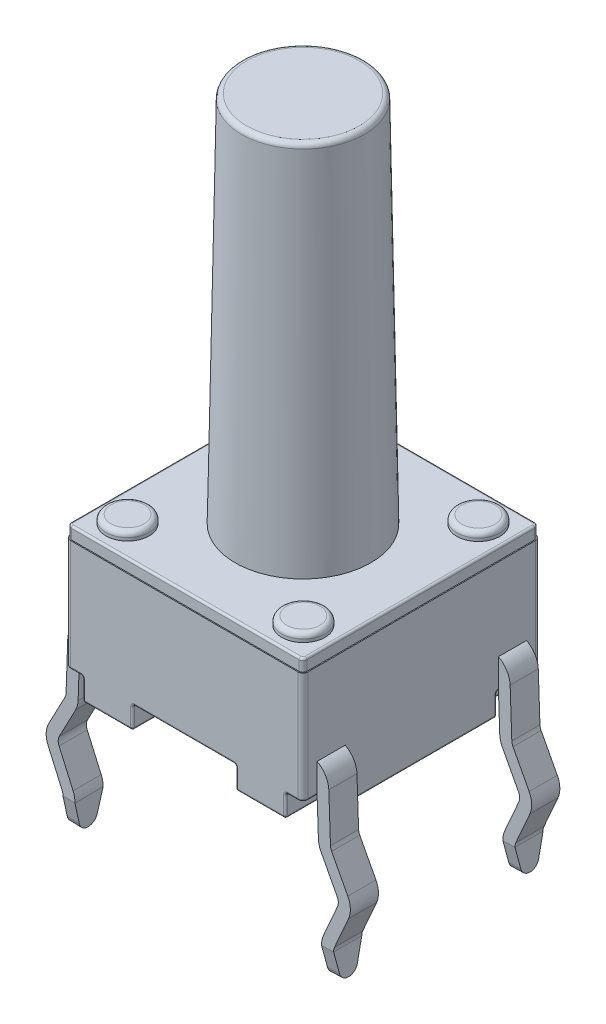
SolidWorks part; units mm, degrees
ref_plane "Front Plane" through (0, 0, 0) normal (0, 0, 1) x (1, 0, 0)
ref_plane "Top Plane" through (0, 0, 0) normal (0, 1, 0) x (1, 0, 0)
ref_plane "Right Plane" through (0, 0, 0) normal (1, 0, 0) x (0, 0, -1)
sketch "Sketch1" plane through (0, 0, 0) normal (0, 1, 0) x (1, 0, 0)
  line L1 (-3.0035, -3.0035) -> (3.0035, -3.0035)
  line L2 (-3.0035, -3.0035) -> (-3.0035, 3.0036)
  line L3 (-3.0035, 3.0036) -> (3.0035, 3.0036)
  line L4 (3.0035, -3.0035) -> (3.0035, 3.0036)
  line L5 (-3.0035, -3.0035) -> (3.0035, 3.0036) construction
  line L6 (-3.0035, 3.0036) -> (3.0035, -3.0035) construction
  point P0 (0, 0)
  dimension "D1" = 6.0071
  dimension "D2" = 6.0071
extrude "Boss-Extrude1" add sketch "Sketch1" along normal blind 2.8194 from offset 0.5588
fillet "Fillet1" radius 0.127 4 edges at (-3.0035, 1.9685, 3.0035) (-3.0035, 1.9685, -3.0036) (3.0035, 1.9685, -3.0036) (3.0035, 1.9685, 3.0035)
sketch "Sketch2" plane through (0, 3.3782, 0) normal (0, -1, 0) x (-1, 0, 0)
  line L8 (2.9781, -2.8765) -> (2.9781, 2.8765)
  line L9 (-2.8765, -2.9781) -> (2.8765, -2.9781)
  line L10 (-2.9781, 2.8765) -> (-2.9781, -2.8765)
  line L11 (2.8765, 2.9782) -> (-2.8765, 2.9782)
  line L12 (2.9781, -2.8765) -> (2.9781, 2.8765)
  line L13 (-2.8765, -2.9781) -> (2.8765, -2.9781)
  line L14 (-2.9781, 2.8765) -> (-2.9781, -2.8765)
  line L15 (2.8765, 2.9782) -> (-2.8765, 2.9782)
  arc A8 (2.8765, -2.9781) -> (2.9781, -2.8765) centre (2.8765, -2.8765) ccw
  arc A9 (-2.9781, -2.8765) -> (-2.8765, -2.9781) centre (-2.8765, -2.8765) ccw
  arc A10 (-2.8765, 2.9782) -> (-2.9781, 2.8765) centre (-2.8765, 2.8766) ccw
  arc A11 (2.9781, 2.8765) -> (2.8765, 2.9782) centre (2.8765, 2.8765) ccw
  arc A12 (2.8765, -2.9781) -> (2.9781, -2.8765) centre (2.8765, -2.8765) ccw
  arc A13 (-2.9781, -2.8765) -> (-2.8765, -2.9781) centre (-2.8765, -2.8765) ccw
  arc A14 (-2.8765, 2.9782) -> (-2.9781, 2.8765) centre (-2.8765, 2.8766) ccw
  arc A15 (2.9781, 2.8765) -> (2.8765, 2.9782) centre (2.8765, 2.8765) ccw
  dimension "D1" = 0.0254
extrude "Boss-Extrude2" add sketch "Sketch2" against normal blind 0.3048
sketch "Sketch3" plane through (0, 0, 0) normal (0, 1, 0) x (1, 0, 0)
  line L0 (-2.5662, -3.0035) -> (-2.5662, -1.8948)
  line L1 (-2.8765, -3.0035) -> (2.8765, -3.0035) construction
  line L2 (-2.5662, -1.8948) -> (-3.0035, -1.8948)
  line L3 (-3.0035, 2.8765) -> (-3.0035, -2.8765) construction
  line L4 (-2.4413, -0.5609) -> (-1.3018, -0.5609)
  line L5 (-1.3018, -0.5609) -> (-1.3017, -3.0035)
  line L6 (-2.4413, -0.5609) -> (-2.4413, 0.5609)
  line L7 (-2.5662, -3.0035) -> (-1.3017, -3.0035)
  line L8 (-3.0035, -1.8948) -> (-3.0035, 1.8948)
  line L9 (-2.4413, 0) -> (-3.0035, 0) construction
  line L10 (-2.5662, 3.0036) -> (-1.3017, 3.0035)
  line L11 (-1.3017, 0.5609) -> (-1.3017, 3.0035)
  line L12 (-2.4413, 0.5609) -> (-1.3017, 0.5609)
  line L13 (-2.5662, 1.8948) -> (-3.0035, 1.8948)
  line L14 (-2.5662, 3.0036) -> (-2.5662, 1.8948)
  line L15 (0, -3.0035) -> (0, 3.0036) construction
  line L16 (2.8765, 3.0036) -> (-2.8765, 3.0036) construction
  line L17 (2.4413, 0) -> (3.0035, 0) construction
  line L18 (2.5662, 3.0035) -> (2.5662, 1.8948)
  line L19 (2.5662, 1.8948) -> (3.0035, 1.8948)
  line L20 (2.4413, 0.5609) -> (1.3017, 0.5609)
  line L21 (1.3017, 0.5609) -> (1.3017, 3.0035)
  line L22 (2.5662, 3.0035) -> (1.3017, 3.0035)
  line L23 (3.0035, -1.8948) -> (3.0035, 1.8948)
  line L24 (2.5662, -3.0036) -> (1.3017, -3.0036)
  line L25 (2.4413, -0.5609) -> (2.4413, 0.5609)
  line L26 (1.3017, -0.5609) -> (1.3017, -3.0036)
  line L27 (2.4413, -0.5609) -> (1.3017, -0.5609)
  line L28 (2.5662, -1.8948) -> (3.0035, -1.8948)
  line L29 (2.5662, -3.0036) -> (2.5662, -1.8948)
  dimension "D1" = 1.7018
extrude "Boss-Extrude3" add sketch "Sketch3" along normal up to next
sketch "Sketch4" plane through (0, 3.683, 0) normal (0, 1, 0) x (1, 0, 0)
  line L1 (-2.2217, -2.2129) -> (2.2217, -2.2129) construction
  line L2 (-2.2217, -2.2129) -> (-2.2217, 2.2129) construction
  line L3 (-2.2217, 2.2129) -> (2.2217, 2.2129) construction
  line L4 (2.2217, -2.2129) -> (2.2217, 2.2129) construction
  line L5 (-2.2217, -2.2129) -> (2.2217, 2.2129) construction
  line L6 (-2.2217, 2.2129) -> (2.2217, -2.2129) construction
  circle A0 centre (2.2217, 2.2129) radius 0.5461
  circle A1 centre (-2.2217, 2.2129) radius 0.5461
  circle A2 centre (-2.2217, -2.2129) radius 0.5461
  circle A3 centre (2.2217, -2.2129) radius 0.5461
  point P0 (0, 0)
  dimension "D1" = 1.0922
extrude "Boss-Extrude4" add sketch "Sketch4" along normal blind 0.2032
sketch "Sketch5" plane through (0, 3.683, 0) normal (0, 1, 0) x (1, 0, 0)
  circle A0 centre (0, 0) radius 1.7145
  dimension "D1" = 3.429
extrude "Boss-Extrude5" add sketch "Sketch5" along normal blind 9.4234 draft 1
fillet "Fillet2" radius 0.127 5 edges at (-2.2217, 3.8862, -1.6668) (-2.2217, 3.8862, 2.759) (2.2217, 3.8862, -1.6668) (2.2217, 3.8862, 2.759) (0, 13.1064, 1.55)
fillet "Fillet3" radius 0.0508 88 edges at (2.9664, 0.5588, 2.9664) (2.9664, 0.5588, -2.9664) (-2.9664, 0.5588, -2.9664) (-2.9664, 0.5588, 2.9664) (3.0035, 0.5588, 2.3857) (3.0035, 0.5588, -2.3857) (1.3017, 0.2794, 3.0036) (1.3017, 0.2794, -3.0035) (2.9484, 3.683, -2.9484) (0, 3.683, -2.9782) (-2.9484, 3.683, -2.9484) (-2.9781, 3.683, 0) (-2.9484, 3.683, 2.9484) (0, 3.683, 2.9781) (2.9484, 3.683, 2.9484) (2.4413, 0.2794, 0.5609) (1.3017, 0.2794, 0.5609) (1.3017, 0.2794, -0.5609) (2.4413, 0.2794, -0.5609) (-1.3018, 0.2794, 0.5609) (-2.4413, 0.2794, 0.5609) (-2.4413, 0.2794, -0.5609) (-1.3017, 0.2794, -0.5609) (2.7849, 0.5588, 1.8948) (3.0035, 0.2794, 1.8948) (2.5662, 0.2794, 3.0036) (2.5662, 0.5588, 2.4492) (2.5662, 0.2794, 1.8948) (3.0035, 0.2794, -1.8948) (2.7849, 0.5588, -1.8948) (2.5662, 0.2794, -1.8948) (2.5662, 0.5588, -2.4492) (2.5662, 0.2794, -3.0035) (-2.5662, 0.2794, -1.8948) (-2.5662, 0.2794, 1.8948) (-1.8715, 0.5588, -0.5609) (-2.4413, 0.5588, 0) (-1.8715, 0.5588, 0.5609) (1.3017, 0.5588, 1.7822) (1.8715, 0.5588, 0.5609) (2.4413, 0.5588, 0) (1.8715, 0.5588, -0.5609) (1.3017, 0.5588, -1.7822) (-1.3017, 0, 1.7822) (-1.8715, 0, 0.5609) (-2.4413, 0, 0) (-1.8715, 0, -0.5609) (-1.3017, 0, -1.7822) (-1.934, 0, -3.0035) (-2.5662, 0, -2.4492) (-2.7849, 0, -1.8948) (-3.0035, 0, 0) (-2.7849, 0, 1.8948) (-2.5662, 0, 2.4492) (-1.934, 0, 3.0035) (1.3017, 0, -1.7822) (1.8715, 0, -0.5609) (2.4413, 0, 0) (1.8715, 0, 0.5609) (1.3017, 0, 1.7822) (1.934, 0, 3.0036) (2.5662, 0, 2.4492) (2.7849, 0, 1.8948) (3.0035, 0, 0) (2.7849, 0, -1.8948) (2.5662, 0, -2.4492) (1.934, 0, -3.0035) (2.9781, 3.683, 0)
sketch "Sketch6" plane through (0, 0, 3.0035) normal (0, 0, 1) x (1, 0, 0)
  line L0 (-2.9873, 1.0641) -> (-3.0423, -0.5107)
  line L1 (-3.0423, -0.5107) -> (-3.5687, -1.5089)
  line L2 (-3.5687, -1.5089) -> (-3.1132, -2.5415)
  line L3 (-3.1132, -2.5415) -> (-3.1424, -3.3782)
  line L4 (-2.9873, 1.0641) -> (-2.5265, 1.0641)
  line L5 (-1.3525, 0) -> (-2.5154, 0) construction
  dimension "D1" = 4.445
  dimension "D2" = 3.3782
  dimension "D3" = 3.0226
  dimension "D4" = 3.5687
  dimension "D5" = 2.032
  dimension "D6" = 1.5748
  dimension "D7" = 92
extrude "Extrude-Thin1" add sketch "Sketch6" against normal blind 0.7112 from offset 0.3556 thin offset against normal yes
sketch "Sketch9" plane through (-3.3254, 0.1161, 0) normal (-0.9994, 0.0349, 0) x (0, 0, 1)
  line L0 (2.6479, -2.7766) -> (2.5175, -3.3091)
  line L1 (2.0672, -3.3091) -> (1.9367, -2.7766)
  line L2 (1.9367, -3.4858) -> (2.6479, -3.4858) construction
  line L3 (2.6479, -2.7766) -> (2.6479, -3.4858)
  line L4 (2.6479, -3.4858) -> (1.9367, -3.4858)
  line L5 (1.9367, -3.4858) -> (1.9367, -2.7766)
  arc A0 (2.5175, -3.3091) -> (2.0672, -3.3091) centre (2.2923, -3.254) cw
  line M1 (2.6479, -3.4858) -> (2.6479, -2.7766)
  line M3 (1.9367, -2.7766) -> (1.9367, -3.4858)
  line M4 (1.9367, -3.4858) -> (2.6479, -3.4858)
extrude "Cut-Extrude1" cut sketch "Sketch9" against normal blind 0.7112 contours L0 A0 L4 M1 | A0 L1 M4 M3
mirror "Mirror1" about plane through (0, 0, 0) normal (0, 0, 1) of "Cut-Extrude1", "Extrude-Thin1"
mirror "Mirror3" about plane through (0, 0, 0) normal (1, 0, 0) of "Mirror1", "Cut-Extrude1", "Extrude-Thin1"
